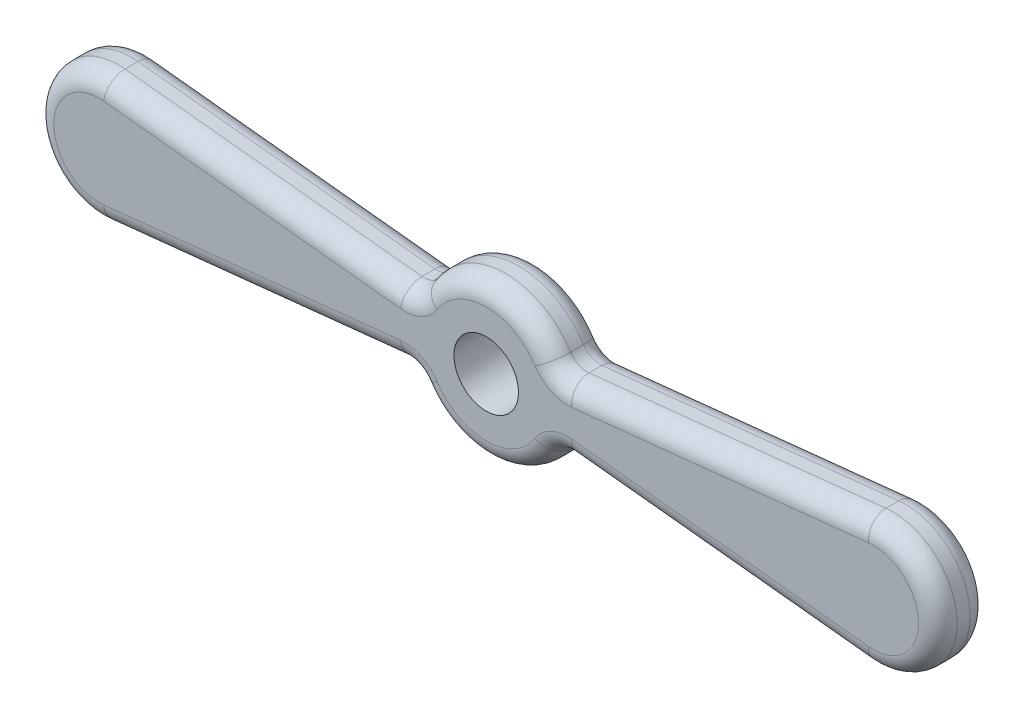
SolidWorks part; units mm, degrees
ref_plane "前基準面" through (0, 0, 0) normal (0, 0, 1) x (1, 0, 0)
ref_plane "上基準面" through (0, 0, 0) normal (0, 1, 0) x (1, 0, 0)
ref_plane "右基準面" through (0, 0, 0) normal (1, 0, 0) x (0, 0, -1)
sketch "草圖1" plane through (0, 0, 0) normal (0, 0, 1) x (1, 0, 0)
  line L0 (0, -36.7106) -> (0, 49.1333) construction
  line L1 (-60, 0) -> (-12, 0) construction
  line L2 (58.9547, 9.9452) -> (10.9539, 4.9001)
  line L3 (58.9547, -9.9452) -> (10.9539, -4.9001)
  line L4 (-60, 0) -> (60, 0) construction
  line L5 (-58.9547, -9.9452) -> (-10.9539, -4.9001)
  line L6 (-58.9547, 9.9452) -> (-10.9539, 4.9001)
  arc A2 (10.9539, 4.9001) -> (-10.9539, 4.9001) centre (0, 0) ccw
  arc A4 (58.9547, -9.9452) -> (58.9547, 9.9452) centre (60, 0) ccw
  arc A5 (-10.9539, -4.9001) -> (10.9539, -4.9001) centre (0, 0) ccw
  arc A6 (-58.9547, -9.9452) -> (-58.9547, 9.9452) centre (-60, 0) cw
  circle A7 centre (0, 0) radius 5
  dimension "D1" = 24
  dimension "D2" = 60
  dimension "D3" = 20
  dimension "D4" = 6
extrude "填料-伸長1" add sketch "草圖1" along normal blind 8
fillet "圓角1" radius 3 4 edges at (-10.9539, 4.9001, 4) (-10.9539, -4.9001, 4) (10.9539, -4.9001, 4) (10.9539, 4.9001, 4)
fillet "圓角2" radius 3 12 edges at (-11.3298, 5.389, 8) (11.3298, 5.389, 8) (11.3298, -5.389, 8) (35.949, -7.5272, 8) (70, 0, 8) (35.949, 7.5272, 8) (0, 12, 8) (-11.3298, -5.389, 8) (0, -12, 8) (-35.949, -7.5272, 8) (-70, 0, 8) (-35.949, 7.5272, 8)
fillet "圓角3" radius 3 12 edges at (-11.3298, 5.389, 0) (0, 12, 0) (11.3298, 5.389, 0) (35.949, 7.5272, 0) (70, 0, 0) (35.949, -7.5272, 0) (11.3298, -5.389, 0) (0, -12, 0) (-11.3298, -5.389, 0) (-35.949, -7.5272, 0) (-70, 0, 0) (-35.949, 7.5272, 0)
